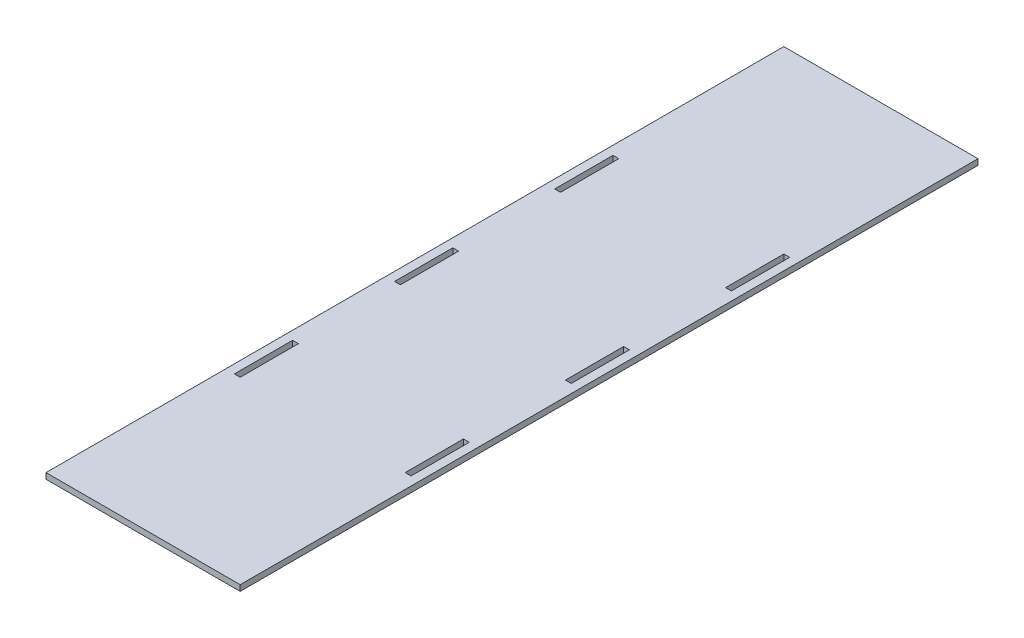
SolidWorks part; units mm, degrees
ref_plane "Alzado" through (0, 0, 0) normal (0, 0, 1) x (1, 0, 0)
ref_plane "Planta" through (0, 0, 0) normal (0, 1, 0) x (1, 0, 0)
ref_plane "Vista lateral" through (0, 0, 0) normal (1, 0, 0) x (0, 0, -1)
sketch "Croquis2" plane through (0, 0, 0) normal (0, 1, 0) x (1, 0, 0)
  line L0 (-42.5, -190) -> (-42.5, 190) construction
  line L1 (-50, -190) -> (50, -190)
  line L2 (-50, -190) -> (-50, 190)
  line L3 (-50, 190) -> (50, 190)
  line L4 (50, -190) -> (50, 190)
  line L5 (-50, -190) -> (50, 190) construction
  line L6 (-50, 190) -> (50, -190) construction
  line L7 (42.5, 190) -> (42.5, -190) construction
  line L8 (0, 190) -> (0, -190) construction
  line L9 (-50, 0) -> (50, 0) construction
  line L10 (-45.5, 97.5) -> (-42.5, 97.5)
  line L11 (-45.5, 97.5) -> (-45.5, 67.5)
  line L12 (-45.5, 67.5) -> (-42.5, 67.5)
  line L13 (-42.5, 97.5) -> (-42.5, 67.5)
  line L14 (-45.5, 97.5) -> (-42.5, 67.5) construction
  line L15 (-45.5, 67.5) -> (-42.5, 97.5) construction
  line L16 (-45.5, 15) -> (-42.5, 15)
  line L17 (-45.5, 15) -> (-45.5, -15)
  line L18 (-45.5, -15) -> (-42.5, -15)
  line L19 (-42.5, 15) -> (-42.5, -15)
  line L20 (-45.5, 15) -> (-42.5, -15) construction
  line L21 (-45.5, -15) -> (-42.5, 15) construction
  line L22 (-45.5, -67.5) -> (-42.5, -67.5)
  line L23 (-45.5, -67.5) -> (-45.5, -97.5)
  line L24 (-45.5, -97.5) -> (-42.5, -97.5)
  line L25 (-42.5, -67.5) -> (-42.5, -97.5)
  line L26 (-45.5, -67.5) -> (-42.5, -97.5) construction
  line L27 (-45.5, -97.5) -> (-42.5, -67.5) construction
  line L28 (42.5, 97.5) -> (45.5, 97.5)
  line L29 (42.5, 97.5) -> (42.5, 67.5)
  line L30 (42.5, 67.5) -> (45.5, 67.5)
  line L31 (45.5, 97.5) -> (45.5, 67.5)
  line L32 (42.5, 97.5) -> (45.5, 67.5) construction
  line L33 (42.5, 67.5) -> (45.5, 97.5) construction
  line L34 (42.5, 15) -> (45.5, 15)
  line L35 (42.5, 15) -> (42.5, -15)
  line L36 (42.5, -15) -> (45.5, -15)
  line L37 (45.5, 15) -> (45.5, -15)
  line L38 (42.5, 15) -> (45.5, -15) construction
  line L39 (42.5, -15) -> (45.5, 15) construction
  line L40 (42.5, -67.5) -> (45.5, -67.5)
  line L41 (42.5, -67.5) -> (42.5, -97.5)
  line L42 (42.5, -97.5) -> (45.5, -97.5)
  line L43 (45.5, -67.5) -> (45.5, -97.5)
  line L44 (42.5, -67.5) -> (45.5, -97.5) construction
  line L45 (42.5, -97.5) -> (45.5, -67.5) construction
  point P0 (0, 0)
  point P12 (-44, 82.5)
  point P19 (-44, 0)
  point P24 (-44, -82.5)
  point P29 (44, 82.5)
  point P34 (44, 0)
  point P39 (44, -82.5)
  dimension "D1" = 100
  dimension "D2" = 380
  dimension "D3" = 30
  dimension "D4" = 3
  dimension "D5" = 30
  dimension "D6" = 30
  dimension "D7" = 30
  dimension "D8" = 30
  dimension "D9" = 30
  dimension "D10" = 42.5
  dimension "D11" = 42.5
  dimension "D12" = 82.5
  dimension "D13" = 82.5
  dimension "D14" = 82.5
  dimension "D15" = 82.5
extrude "Saliente-Extruir1" add sketch "Croquis2" along normal blind 3
